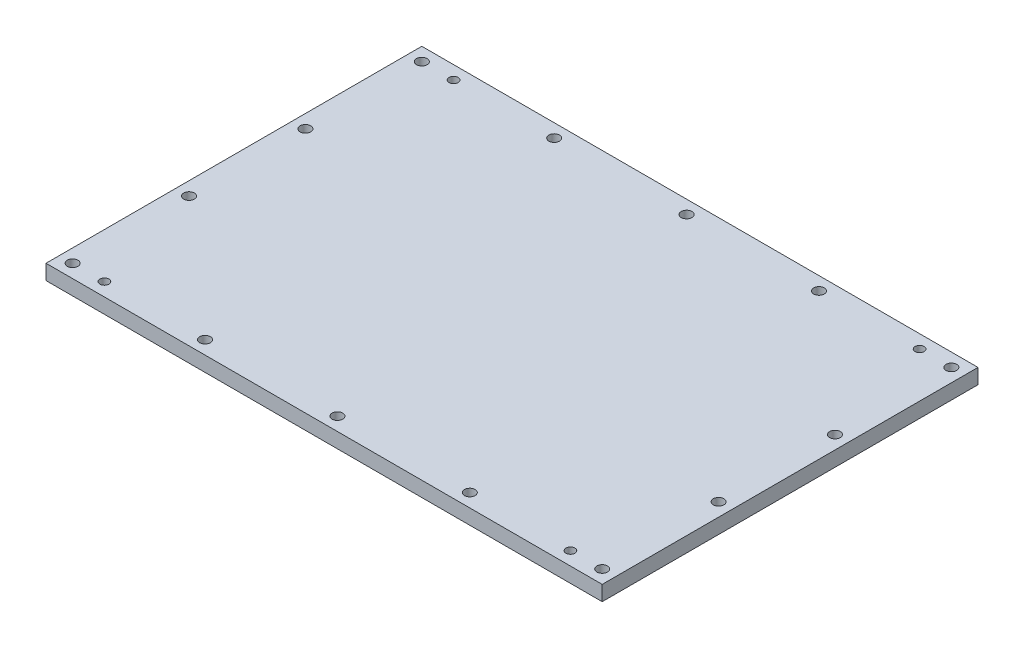
SolidWorks part; units mm, degrees
material "Acrylic (Medium-high impact)"
ref_plane "Front Plane" through (0, 0, 0) normal (0, 0, 1) x (1, 0, 0)
ref_plane "Top Plane" through (0, 0, 0) normal (0, 1, 0) x (1, 0, 0)
ref_plane "Right Plane" through (0, 0, 0) normal (1, 0, 0) x (0, 0, -1)
sketch "Sketch1" plane through (0, 0, 0) normal (0, 1, 0) x (1, 0, 0)
  line L0 (0, 0) -> (0, 54.643) construction
  line L1 (-117.475, 79.375) -> (117.475, 79.375)
  line L2 (-117.475, 79.375) -> (-117.475, -79.375)
  line L3 (-117.475, -79.375) -> (117.475, -79.375)
  line L4 (117.475, 79.375) -> (117.475, -79.375)
  line L5 (0, 0) -> (58.7533, 0) construction
  dimension "D1" = 158.75
  dimension "D2" = 234.95
extrude "Boss-Extrude1" add sketch "Sketch1" along normal blind 6.35
hole_wizard "#8 Clearance Hole1" positions "Sketch4" profile "Sketch3" hole size "#8" standard "ANSI Inch" end condition through all
sketch "Sketch4" plane through (0, 6.35, 0) normal (0, 1, 0) x (1, 0, 0)
  line L0 (-111.8489, -73.7489) -> (-111.8489, -24.583) construction
  line L3 (-111.8489, -24.583) -> (-111.8489, 24.583) construction
  line L6 (-111.8489, 24.583) -> (-111.8489, 73.7489) construction
  line L9 (-111.8489, 73.7489) -> (-55.9245, 73.7489) construction
  line L12 (-55.9245, 73.7489) -> (0, 73.7489) construction
  line L15 (117.475, 79.375) -> (-117.475, 79.375) construction
  line L16 (-111.8489, 73.7489) -> (-111.8489, 79.375) construction
  line L19 (-111.8489, 73.7489) -> (-117.475, 73.7489) construction
  line L20 (-117.475, 79.375) -> (-117.475, -79.375) construction
  line L23 (0, 0) -> (38.1943, 0) construction
  line L26 (0, 0) -> (0, 43.1154) construction
  point P0 (0, 73.7489)
  point P2 (-55.9245, 73.7489)
  point P4 (-111.8489, 73.7489)
  point P6 (-111.8489, 24.583)
  point P8 (-111.8489, -24.583)
  point P10 (-111.8489, -73.7489)
  point P77 (111.8489, -73.7489)
  point P78 (111.8489, -24.583)
  point P79 (111.8489, 24.583)
  point P80 (55.9245, 73.7489)
  point P81 (111.8489, 73.7489)
  point P82 (55.9245, -73.7489)
  point P83 (0, -73.7489)
  point P84 (-55.9245, -73.7489)
  dimension "D1" = 5.6261
sketch "Sketch3" plane through (0, 6.35, -73.7489) normal (1, 0, 0) x (0, 0, 1)
  line L0 (0, 0) -> (0, 6.35)
  line L1 (0, 6.35) -> (2.2479, 6.35)
  line L2 (2.2479, 6.35) -> (2.2479, 0)
  line L5 (2.2479, 0) -> (0, 0)
  line L11 (0, -6.35) -> (0, 107.95) construction
  dimension "Thru Hole Dia." = 4.4958
  dimension "Thru Hole Depth" = 6.35
hole_wizard "#6 Clearance Hole1" positions "Sketch6" profile "Sketch5" hole size "#6" standard "ANSI Inch" end condition through all
sketch "Sketch6" plane through (0, 6.35, 0) normal (0, 1, 0) x (1, 0, 0)
  line L0 (-111.8489, 73.7489) -> (-55.9245, 73.7489) construction
  line L1 (0, 0) -> (0, 42.6836) construction
  line L4 (0, 0) -> (43.1778, 0) construction
  line L5 (-117.475, 79.375) -> (-117.475, -79.375) construction
  point P7 (-98.425, 73.7489)
  point P23 (-98.425, -73.7489)
  point P24 (98.425, 73.7489)
  point P25 (98.425, -73.7489)
  dimension "D1" = 19.05
sketch "Sketch5" plane through (-98.425, 6.35, -73.7489) normal (1, 0, 0) x (0, 0, 1)
  line L0 (0, 0) -> (0, 6.35)
  line L1 (0, 6.35) -> (1.8986, 6.35)
  line L2 (1.8986, 6.35) -> (1.8986, 0)
  line L5 (1.8986, 0) -> (0, 0)
  line L11 (0, -6.35) -> (0, 107.95) construction
  dimension "Thru Hole Dia." = 3.7973
  dimension "Thru Hole Depth" = 6.35
